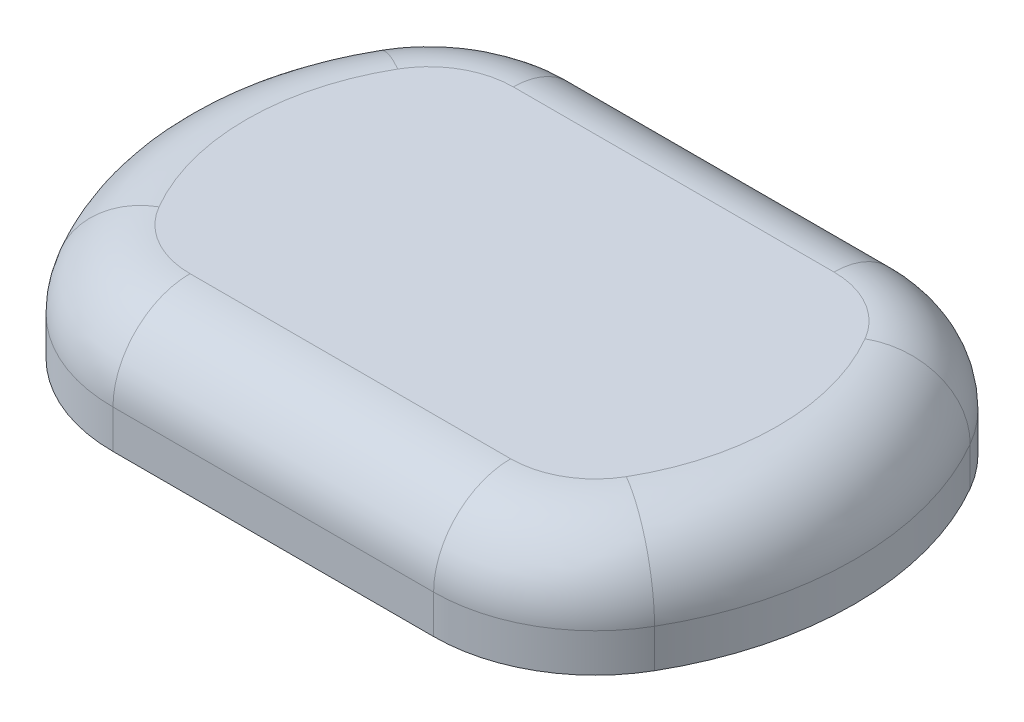
SolidWorks part; units mm, degrees
material "ABS"
ref_plane "前视基准面" through (0, 0, 0) normal (0, 0, 1) x (1, 0, 0)
ref_plane "上视基准面" through (0, 0, 0) normal (0, 1, 0) x (1, 0, 0)
ref_plane "右视基准面" through (0, 0, 0) normal (1, 0, 0) x (0, 0, -1)
sketch "草图1" plane through (0, 0, 0) normal (0, 1, 0) x (1, 0, 0)
  line L0 (-52.2, 20.7111) -> (36.8, 20.7111)
  line L1 (36.8, 20.7111) -> (36.8, -41.2889)
  line L2 (36.8, -41.2889) -> (-52.2, -41.2889)
  line L3 (-52.2, 20.7111) -> (-52.2, -41.2889)
  dimension "D1" = 89
  dimension "D2" = 62
extrude "凸台-拉伸1" add sketch "草图1" along normal blind 15
sketch "草图2" plane through (0, 15, 0) normal (0, 1, 0) x (1, 0, 0)
  line L1 (36.8, 20.7111) -> (-52.2, 20.7111) construction
  line L7 (-28.5205, 20.7111) -> (13.1205, 20.7111)
  line L8 (-52.2, -10.2889) -> (37.4271, -10.2889) construction
  line L9 (-52.2, 20.7111) -> (-52.2, -41.2889) construction
  line L10 (-28.5205, -41.2889) -> (13.1205, -41.2889)
  line L11 (-7.7, 20.7111) -> (-7.7, -51.3025) construction
  line L14 (-68.5146, 33.8822) -> (45.8307, 33.8822)
  line L15 (-68.5146, 33.8822) -> (-68.5146, -48.859)
  line L16 (-68.5146, -48.859) -> (45.8307, -48.859)
  line L17 (45.8307, 33.8822) -> (45.8307, -48.859)
  arc A0 (-46.707, 10.2111) -> (-46.707, -30.7889) centre (-11.2, -10.2889) ccw
  arc A1 (-28.5205, 20.7111) -> (-46.707, 10.2111) centre (-28.5205, -0.2889) ccw
  arc A3 (-28.5205, -41.2889) -> (-46.707, -30.7889) centre (-28.5205, -20.2889) cw
  arc A4 (13.1205, -41.2889) -> (31.307, -30.7889) centre (13.1205, -20.2889) ccw
  arc A5 (31.307, 10.2111) -> (31.307, -30.7889) centre (-4.2, -10.2889) cw
  arc A6 (13.1205, 20.7111) -> (31.307, 10.2111) centre (13.1205, -0.2889) cw
  point P16 (-52.2, -10.2889)
  dimension "D3" = 82
  dimension "D1" = 21
  dimension "D2" = 21
extrude "切除-拉伸2" cut sketch "草图2" against normal up to next
fillet "圆角1" radius 10 8 edges at (36.8, 15, 10.2889) (23.6205, 15, 38.4754) (-7.7, 15, 41.2889) (-39.0205, 15, 38.4754) (-52.2, 15, 10.2889) (-39.0205, 15, -17.8976) (-7.7, 15, -20.7111) (23.6205, 15, -17.8976)
